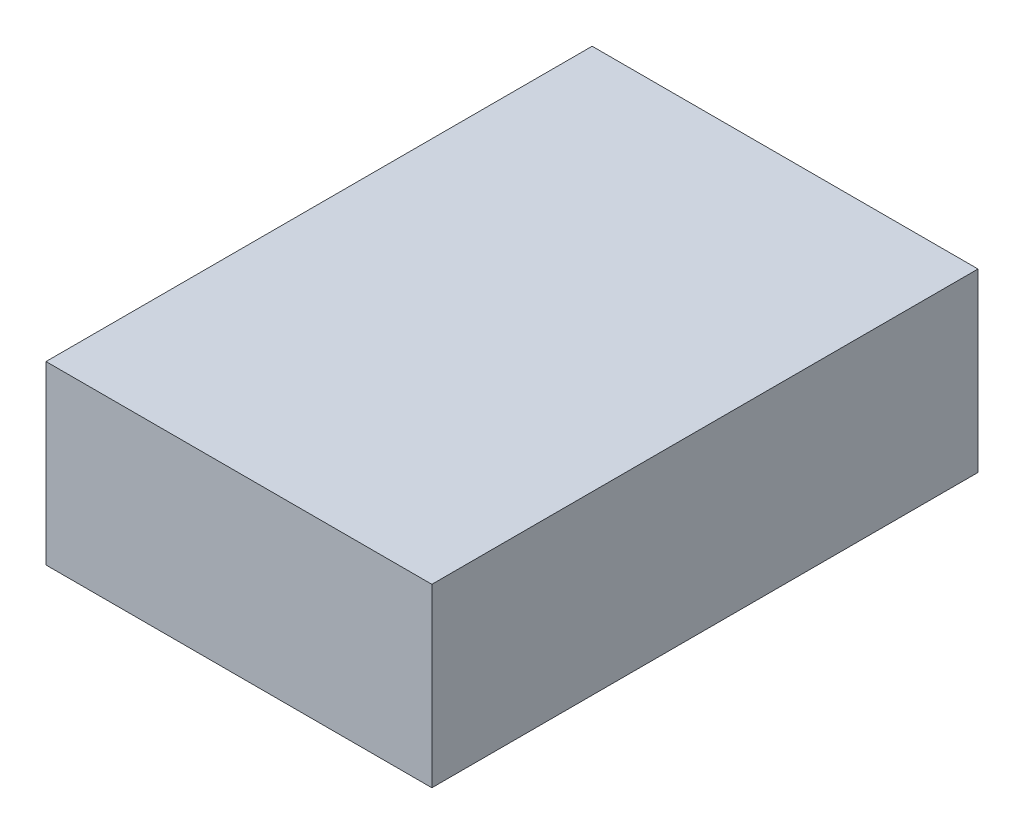
SolidWorks part; units mm, degrees
ref_plane "Front Plane" through (0, 0, 0) normal (0, 0, 1) x (1, 0, 0)
ref_plane "Top Plane" through (0, 0, 0) normal (0, 1, 0) x (1, 0, 0)
ref_plane "Right Plane" through (0, 0, 0) normal (1, 0, 0) x (0, 0, -1)
sketch "Sketch1" plane through (0, 0, 0) normal (0, 1, 0) x (1, 0, 0)
  line L1 (25.4, 35.95) -> (-25.4, 35.95)
  line L2 (25.4, 35.95) -> (25.4, -35.95)
  line L3 (25.4, -35.95) -> (-25.4, -35.95)
  line L4 (-25.4, 35.95) -> (-25.4, -35.95)
  line L5 (25.4, 35.95) -> (-25.4, -35.95) construction
  line L6 (25.4, -35.95) -> (-25.4, 35.95) construction
  point P0 (0, 0)
  dimension "D1" = 50.8
  dimension "D2" = 71.9
extrude "Boss-Extrude1" add sketch "Sketch1" along normal blind 23.2
